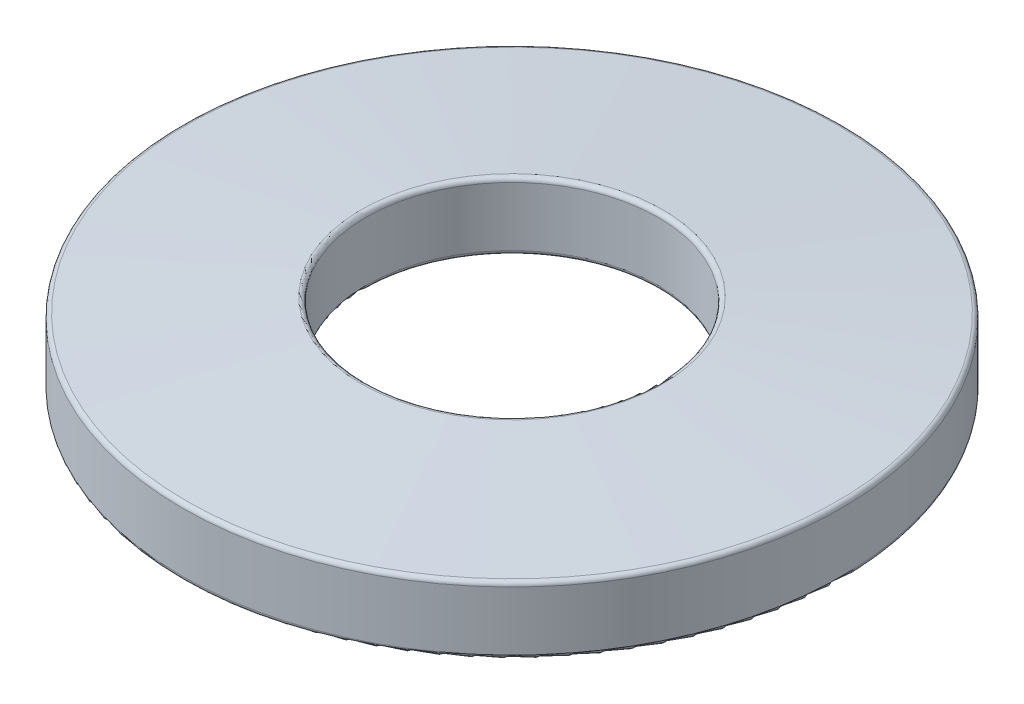
SolidWorks part; units mm, degrees
ref_plane "Front Plane" through (0, 0, 0) normal (0, 0, 1) x (1, 0, 0)
ref_plane "Top Plane" through (0, 0, 0) normal (0, 1, 0) x (1, 0, 0)
ref_plane "Right Plane" through (0, 0, 0) normal (1, 0, 0) x (0, 0, -1)
sketch "Sketch2" plane through (0, 0, 0) normal (1, 0, 0) x (0, 0, -1)
  line L0 (-8.5598, 0) -> (8.5598, 0) construction
  line L1 (8.5598, 4.826) -> (8.5598, 0.8636)
  line L2 (8.5598, 0) -> (19.304, 0) construction
  line L3 (8.5598, 0) -> (8.5598, 4.826) construction
  line L4 (8.5598, 4.826) -> (19.304, 4.826) construction
  line L5 (19.304, 0) -> (19.304, 4.826) construction
  line L6 (19.304, 0) -> (19.304, 3.9624)
  line L7 (8.5598, 4.826) -> (19.304, 3.9624)
  line L8 (19.304, 0) -> (8.5598, 0.8636)
  line L9 (0, 0) -> (0, 11.9435) construction
  point P4 (0, 0)
  dimension "D1" = 17.1196
  dimension "D2" = 19.304
  dimension "D3" = 4.826
  dimension "D4" = 3.9624
  dimension "D5" = 3.9624
revolve "Revolve1" add sketch "Sketch2" angle 360 about L9
fillet "Fillet1" radius 0.254 4 edges at (0, 0, -19.304) (0, 3.9624, -19.304) (0, 0.8636, -8.5598) (0, 4.826, -8.5598)
